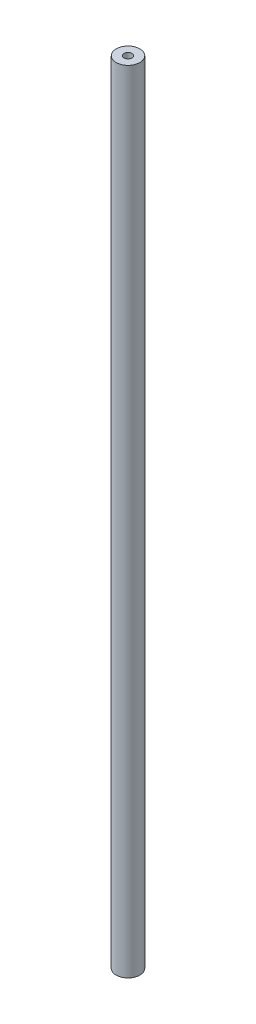
SolidWorks part; units mm, degrees
ref_plane "Front Plane" through (0, 0, 0) normal (0, 0, 1) x (1, 0, 0)
ref_plane "Top Plane" through (0, 0, 0) normal (0, 1, 0) x (1, 0, 0)
ref_plane "Right Plane" through (0, 0, 0) normal (1, 0, 0) x (0, 0, -1)
sketch "Sketch1" plane through (0, 0, 0) normal (0, 1, 0) x (1, 0, 0)
  circle A0 centre (0, 0) radius 1.5
  circle A1 centre (0, 0) radius 0.5
  dimension "D1" = 1
  dimension "D2" = 3
sketch "Sketch2" plane through (0, 0, 0) normal (0, 0, 1) x (1, 0, 0)
  line L0 (0, 50.0002) -> (0, -50.0002)
  line L3 (0, 50.0002) -> (0, 75.0002) construction
  line L4 (0, -50.0002) -> (0, -75.0002) construction
  line L5 (-0.0625, -125.0002) -> (0.0625, -75.0004) construction
  line L6 (0.0625, -75.0004) -> (0.375, 49.9992) construction
  line L7 (0.4375, 74.9991) -> (0.5625, 124.999) construction
  line L8 (0.0625, -75.0004) -> (0, -75.0002) construction
  line L9 (0.5625, 124.999) -> (0.0625, 125.0002) construction
  line L10 (0.4375, 74.9991) -> (0, 75.0002) construction
  line L11 (0, 50.0002) -> (0.375, 49.9992) construction
  line L12 (0.375, 49.9992) -> (0.4375, 74.9991) construction
  arc A1 (0, 75.0002) -> (0.0625, 125.0002) centre (20000.0547, 75.0002) cw construction
  arc A2 (0, -75.0002) -> (-0.0625, -125.0002) centre (-20000.0547, -75.0002) cw construction
  point P9 (4.3311, 50.3672)
  point P13 (5.2462, 50.3356)
  point P14 (4.8744, 49.6708)
  point P15 (2.3985, 74.9424)
  point P16 (0, 0)
  dimension "D1" = 50
  dimension "D2" = 25
  dimension "D3" = 150
  dimension "D4" = 0.5
sweep "Sweep1" add profiles "Sketch1" path "Sketch2"
